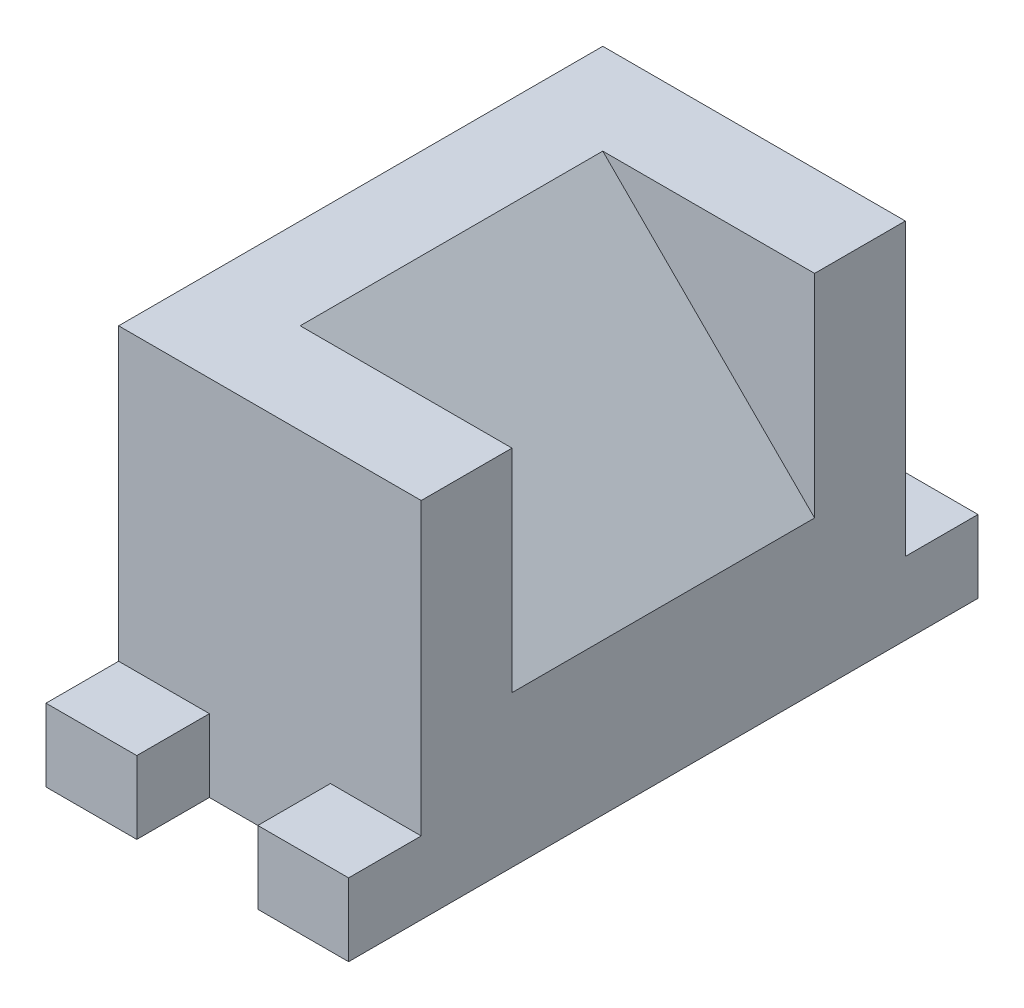
SolidWorks part; units mm, degrees
ref_plane "Ön Düzlem" through (0, 0, 0) normal (0, 0, 1) x (1, 0, 0)
ref_plane "Üst Düzlem" through (0, 0, 0) normal (0, 1, 0) x (1, 0, 0)
ref_plane "Sağ Düzlem" through (0, 0, 0) normal (1, 0, 0) x (0, 0, -1)
sketch "Çizim1" plane through (0, 0, 0) normal (0, 1, 0) x (1, 0, 0)
  line L1 (-25, 40) -> (25, 40)
  line L2 (-25, 40) -> (-25, -40)
  line L3 (-25, -40) -> (25, -40)
  line L4 (25, 40) -> (25, -40)
  line L5 (-25, 40) -> (25, -40) construction
  line L6 (-25, -40) -> (25, 40) construction
  point P0 (0, 0)
  dimension "D1" = 80
  dimension "D2" = 50
extrude "Yükseklik-Ekstrüzyon2" add sketch "Çizim1" along normal blind 60
sketch "Çizim2" plane through (0, 0, 40) normal (0, 0, 1) x (1, 0, 0)
  line L0 (0, 0) -> (0, 27.4184) construction
  line L1 (-25, 0) -> (-10, 0)
  line L2 (-25, 0) -> (-25, 12)
  line L3 (-25, 12) -> (-10, 12)
  line L4 (-10, 0) -> (-10, 12)
  dimension "D1" = 15
  dimension "D2" = 12
extrude "Yükseklik-Ekstrüzyon3" add sketch "Çizim2" along normal blind 12
mirror "Aynalama1" about plane through (0, 0, 0) normal (1, 0, 0) of "Yükseklik-Ekstrüzyon3"
mirror "Aynalama2" about plane through (0, 0, 0) normal (0, 0, 1) of "Aynalama1", "Yükseklik-Ekstrüzyon3"
ref_plane "Düzlem1" through (0, 0, 25) normal (0, 0, 1) x (1, 0, 0)
sketch "Çizim3" plane through (0, 0, 25) normal (0, 0, 1) x (1, 0, 0)
  line L0 (-10, 60) -> (25, 25)
  line L1 (-25, 60) -> (25, 60) construction
  line L2 (25, 60) -> (25, 12) construction
  line L3 (25, 25) -> (25, 60)
  line L4 (25, 60) -> (-10, 60)
  dimension "D1" = 35
  dimension "D2" = 35
extrude "Kes-Ekstrüzyon1" cut sketch "Çizim3" against normal blind 50
